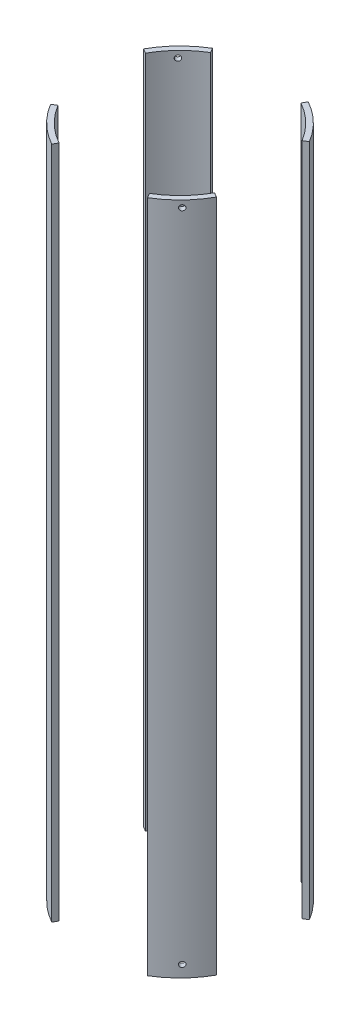
SolidWorks part; units mm, degrees
ref_plane "Front Plane" through (0, 0, 0) normal (0, 0, 1) x (1, 0, 0)
ref_plane "Top Plane" through (0, 0, 0) normal (0, 1, 0) x (1, 0, 0)
ref_plane "Right Plane" through (0, 0, 0) normal (1, 0, 0) x (0, 0, -1)
sketch "Sketch2" plane through (0, 0, 0) normal (0, 1, 0) x (1, 0, 0)
  circle A0 centre (0, 0) radius 88.9
  circle A1 centre (0, 0) radius 83.82
  dimension "D1" = 177.8
  dimension "D2" = 167.64
extrude "Boss-Extrude1" add sketch "Sketch2" along normal mid plane 635
sketch "Sketch3" plane through (0, 0, 0) normal (0, 1, 0) x (1, 0, 0)
  line L0 (0, 0) -> (169.6618, 101.6776)
  line L1 (-58.1167, 96.9749) -> (0, 0)
  line L2 (0, 0) -> (53.9, 96.9749)
  line L3 (53.9, 96.9749) -> (-58.1167, 96.9749)
  line L4 (0, 0) -> (70.9917, -118.4586)
  line L5 (70.9917, -118.4586) -> (-65.8409, -118.4586)
  line L6 (-65.8409, -118.4586) -> (0, 0)
  line L7 (169.6618, 101.6776) -> (169.6618, -94.3004)
  line L8 (169.6618, -94.3004) -> (0, 0)
  line L9 (0, 0) -> (-123.7413, 68.7771)
  line L10 (-123.7413, 68.7771) -> (-123.7413, -74.1577)
  line L11 (-123.7413, -74.1577) -> (0, 0)
  dimension "D1" = 60
  dimension "D2" = 60
  dimension "D3" = 60
  dimension "D4" = 60
  dimension "D5" = 30
  dimension "D6" = 30
extrude "Cut-Extrude1" cut sketch "Sketch3" against normal through all both and the other way through all contours L8 L7 L0 | L2 L3 L1 | L10 L11 L9 | L6 L5 L4
ref_plane "Bolt reference plane" through (-56.3092, 0, 58.1758) normal (0.6955, 0, -0.7185) x (-0.7185, 0, -0.6955)
sketch "Sketch5" plane through (-56.3092, 0, 58.1758) normal (0.6955, 0, -0.7185) x (-0.7185, 0, -0.6955)
  line L0 (-23.009, -317.5) -> (23.009, -317.5) construction
  circle A0 centre (-0.0228, 311.15) radius 2.54
  circle A1 centre (-0.0228, -306.3875) radius 2.54
  point P6 (0, 0)
  dimension "D1" = 5.08
  dimension "D4" = 11.1125
  dimension "D2" = 21.717
  dimension "D3" = 6.35
extrude "Bolt holes" cut sketch "Sketch5" against normal through all
pattern_circular "Bolt pattern" count 4 over 360 about axis through (0, 317.5, 0) along (0, 1, 0) of "Bolt holes"
equation "\"D1@Boss-Extrude1\"=3*12"
